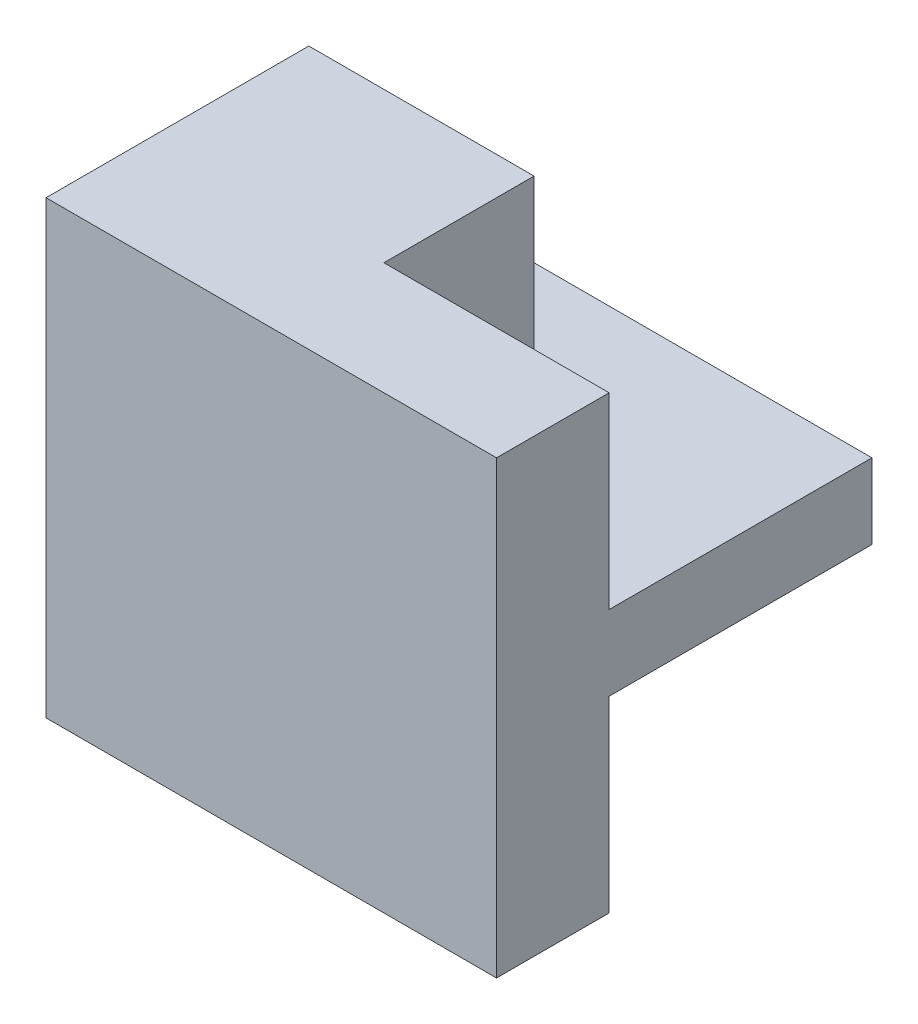
SolidWorks part; units mm, degrees
ref_plane "Front Plane" through (0, 0, 0) normal (0, 0, 1) x (1, 0, 0)
ref_plane "Top Plane" through (0, 0, 0) normal (0, 1, 0) x (1, 0, 0)
ref_plane "Right Plane" through (0, 0, 0) normal (1, 0, 0) x (0, 0, -1)
sketch "Sketch1" plane through (0, 0, 0) normal (0, 1, 0) x (1, 0, 0)
  line L1 (-3, -2.5) -> (3, -2.5)
  line L2 (-3, -2.5) -> (-3, 2.5)
  line L3 (-3, 2.5) -> (3, 2.5)
  line L4 (3, -2.5) -> (3, 2.5)
  line L5 (-3, -2.5) -> (3, 2.5) construction
  line L6 (-3, 2.5) -> (3, -2.5) construction
  point P0 (0, 0)
  dimension "D1" = 5
  dimension "D2" = 6
extrude "Boss-Extrude1" add sketch "Sketch1" along normal blind 6
sketch "Sketch2" plane through (0, 6, 0) normal (0, 1, 0) x (1, 0, 0)
  line L0 (3, -1) -> (0, -1)
  line L1 (3, -2.5) -> (3, 2.5) construction
  line L2 (0, -1) -> (0, 1)
  line L3 (0, 1) -> (-3, 1)
  line L4 (-3, 2.5) -> (-3, -2.5) construction
  line L5 (-3, 1) -> (-3, -2.5)
  line L6 (-3, -2.5) -> (3, -2.5)
  line L7 (3, -2.5) -> (3, -1)
  line M7 (3, -2.5) -> (3, 2.5)
  line M8 (3, 2.5) -> (-3, 2.5)
  line M9 (-3, 2.5) -> (-3, -2.5)
  dimension "D1" = 1.5
  dimension "D2" = 3.5
  dimension "D3" = 3
extrude "Cut-Extrude1" cut sketch "Sketch2" against normal blind 2.5 contours L3 L2 L0 M7 M8 M9
sketch "Sketch3" plane through (0, 0, 0) normal (0, -1, 0) x (1, 0, 0)
  line L0 (3, 1) -> (0, 1)
  line L1 (0, 1) -> (0, -1)
  line L2 (0, -1) -> (-3, -1)
  line L3 (-3, -1) -> (-3, 2.5)
  line L4 (-3, 2.5) -> (3, 2.5)
  line L5 (3, 2.5) -> (3, 1)
  line M7 (3, -2.5) -> (3, 2.5)
  line M9 (-3, 2.5) -> (-3, -2.5)
  line M10 (-3, -2.5) -> (3, -2.5)
extrude "Cut-Extrude2" cut sketch "Sketch3" against normal blind 2.5 contours L1 L2 L0 M9 M10 M7
